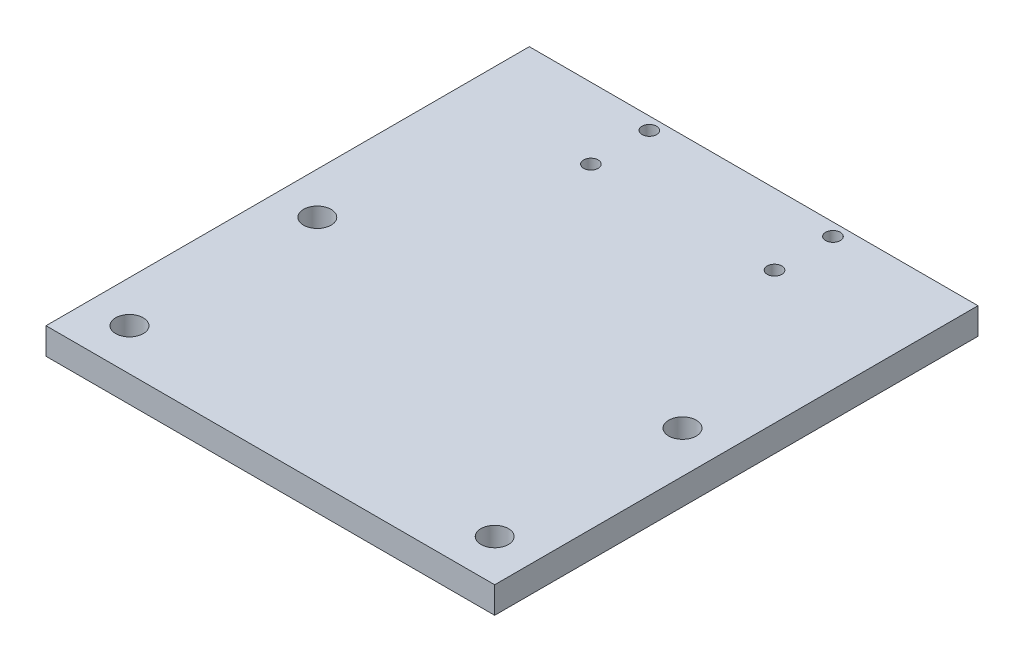
SolidWorks part; units mm, degrees
ref_plane "Front Plane" through (0, 0, 0) normal (0, 0, 1) x (1, 0, 0)
ref_plane "Top Plane" through (0, 0, 0) normal (0, 1, 0) x (1, 0, 0)
ref_plane "Right Plane" through (0, 0, 0) normal (1, 0, 0) x (0, 0, -1)
sketch "Sketch1" plane through (0, 0, 0) normal (0, 1, 0) x (1, 0, 0)
  line L0 (75.75, 112.8) -> (31.75, 112.8) construction
  line L1 (0, 0) -> (107.5, 0)
  line L2 (0, 0) -> (0, 115.8)
  line L3 (0, 115.8) -> (107.5, 115.8)
  line L4 (107.5, 0) -> (107.5, 115.8)
  circle A0 centre (31.75, 112.8) radius 1.75
  circle A1 centre (75.75, 98.8) radius 1.75
  circle A2 centre (31.75, 98.8) radius 1.75
  circle A3 centre (75.75, 112.8) radius 1.75
  circle A4 centre (10, 55) radius 3.3
  circle A5 centre (97.5, 55) radius 3.3
  circle A6 centre (10, 10) radius 3.3
  circle A7 centre (97.5, 10) radius 3.3
  point P11 (53.75, 112.8)
  point P12 (53.75, 115.8)
  point P23 (0, 0)
  point P24 (0, 0)
  point P25 (0, 0)
  point P26 (0, 0)
  dimension "D3" = 3.5
  dimension "D6" = 115.8
  dimension "D10" = 6.6
  dimension "D1" = 14
  dimension "D2" = 44
  dimension "D4" = 107.5
  dimension "D5" = 3
  dimension "D7" = 10
  dimension "D8" = 10
  dimension "D9" = 10
  dimension "D11" = 45
extrude "Boss-Extrude1" add sketch "Sketch1" along normal blind 6.35
